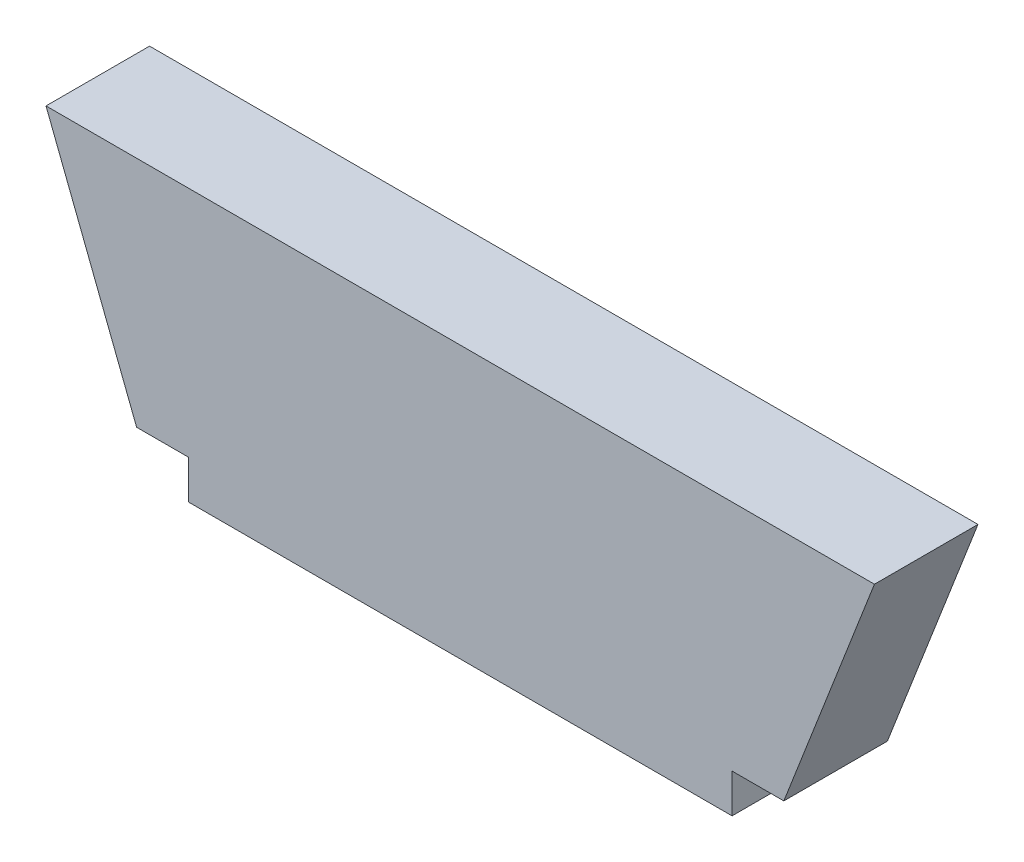
SolidWorks part; units mm, degrees
material "Стекло"
ref_plane "Спереди" through (0, 0, 0) normal (0, 0, 1) x (1, 0, 0)
ref_plane "Сверху" through (0, 0, 0) normal (0, 1, 0) x (1, 0, 0)
ref_plane "Справа" through (0, 0, 0) normal (1, 0, 0) x (0, 0, -1)
sketch "Эскиз1" plane through (0, 0, 0) normal (0, 0, 1) x (1, 0, 0)
  line L0 (0, 33.2005) -> (0, -37.6342) construction
  line L1 (-25, 0) -> (25, 0) construction
  line L2 (-32, 18) -> (32, 18)
  line L3 (-25, 0) -> (-32, 18)
  line L4 (25, 0) -> (32, 18)
  line L7 (-21, -3) -> (21, -3)
  line L8 (25, 0) -> (21, 0)
  line L9 (21, 0) -> (21, -3)
  line L10 (-25, 0) -> (-21, 0)
  line L11 (-21, 0) -> (-21, -3)
  dimension "D7" = 3
  dimension "D1" = 50
  dimension "D2" = 3
  dimension "D3" = 32
  dimension "D4" = 64
  dimension "D5" = 4
  dimension "D6" = 4
  dimension "D9" = 18
extrude "Бобышка-Вытянуть1" add sketch "Эскиз1" along normal blind 8
